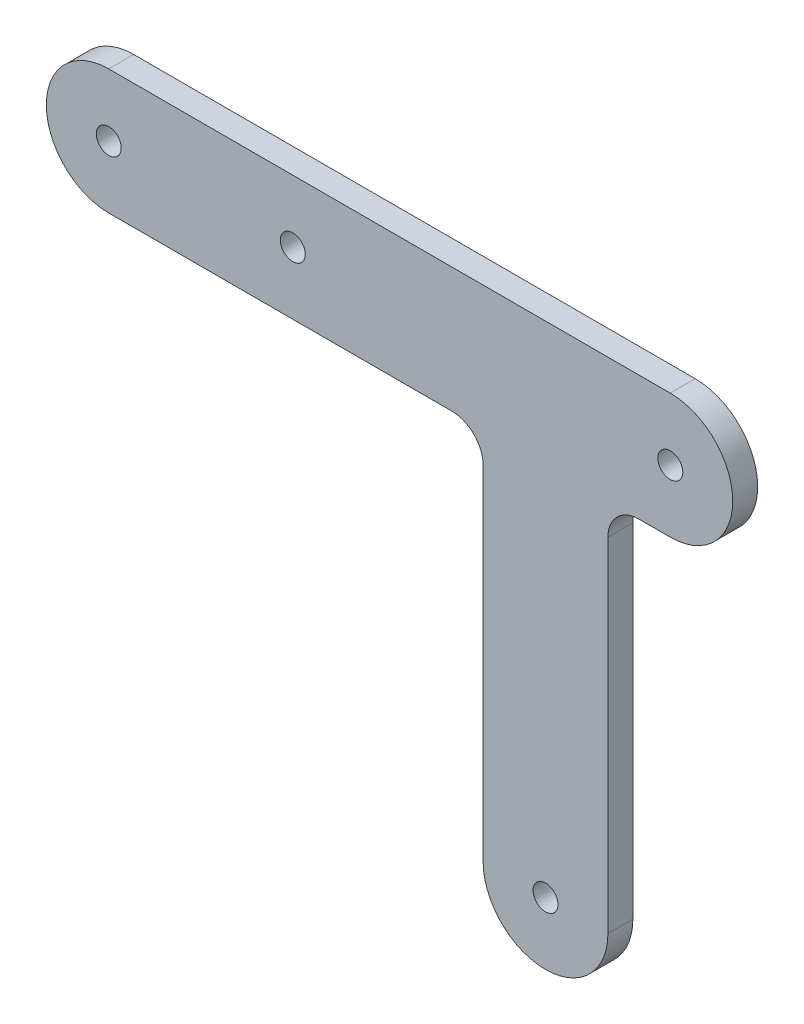
SolidWorks part; units mm, degrees
ref_plane "前视基准面" through (0, 0, 0) normal (0, 0, 1) x (1, 0, 0)
ref_plane "上视基准面" through (0, 0, 0) normal (0, 1, 0) x (1, 0, 0)
ref_plane "右视基准面" through (0, 0, 0) normal (1, 0, 0) x (0, 0, -1)
sketch "草图1" plane through (0, 0, 0) normal (0, 0, 1) x (1, 0, 0)
  line L0 (-43.1082, -15.6781) -> (-98.1082, -15.6781)
  line L1 (-8.1082, -15.6781) -> (-13.1082, -15.6781)
  line L3 (-8.1082, 4.3219) -> (-98.1082, 4.3219)
  line L13 (-38.1082, -20.6781) -> (-38.1082, -75.6781)
  line L15 (-18.1082, -20.6781) -> (-18.1082, -75.6781)
  arc A0 (-98.1082, 4.3219) -> (-98.1082, -15.6781) centre (-98.1082, -5.6781) ccw
  arc A1 (-8.5928, -15.6663) -> (-1.9798, 2.224) centre (-8.1082, -5.6781) ccw
  circle A2 centre (-98.1082, -5.6781) radius 2
  circle A5 centre (-8.1082, -5.6781) radius 2
  arc A6 (-8.5928, -15.6663) -> (-8.1082, 4.3219) centre (-8.1082, -5.6781) ccw
  circle A7 centre (-68.6082, -5.6781) radius 2
  arc A8 (-38.1082, -75.6781) -> (-18.1082, -75.6781) centre (-28.1082, -75.6781) ccw
  circle A9 centre (-28.1082, -75.6781) radius 2
  arc A10 (-38.1082, -20.6781) -> (-43.1082, -15.6781) centre (-43.1082, -20.6781) ccw
  arc A11 (-13.1082, -15.6781) -> (-18.1082, -20.6781) centre (-13.1082, -20.6781) ccw
  point P0 (0, 0)
  point P22 (-38.1082, -15.6781)
  dimension "D1" = 90
  dimension "D2" = 10
  dimension "D4" = 10
  dimension "D5" = 4
  dimension "D6" = 4
  dimension "D7" = 60.5
  dimension "D8" = 20
  dimension "D9" = 10
  dimension "D10" = 4
  dimension "D11" = 4
  dimension "D12" = 5
  dimension "D13" = 5
  dimension "D3" = 20
extrude "凸台-拉伸1" add sketch "草图1" along normal blind 4
